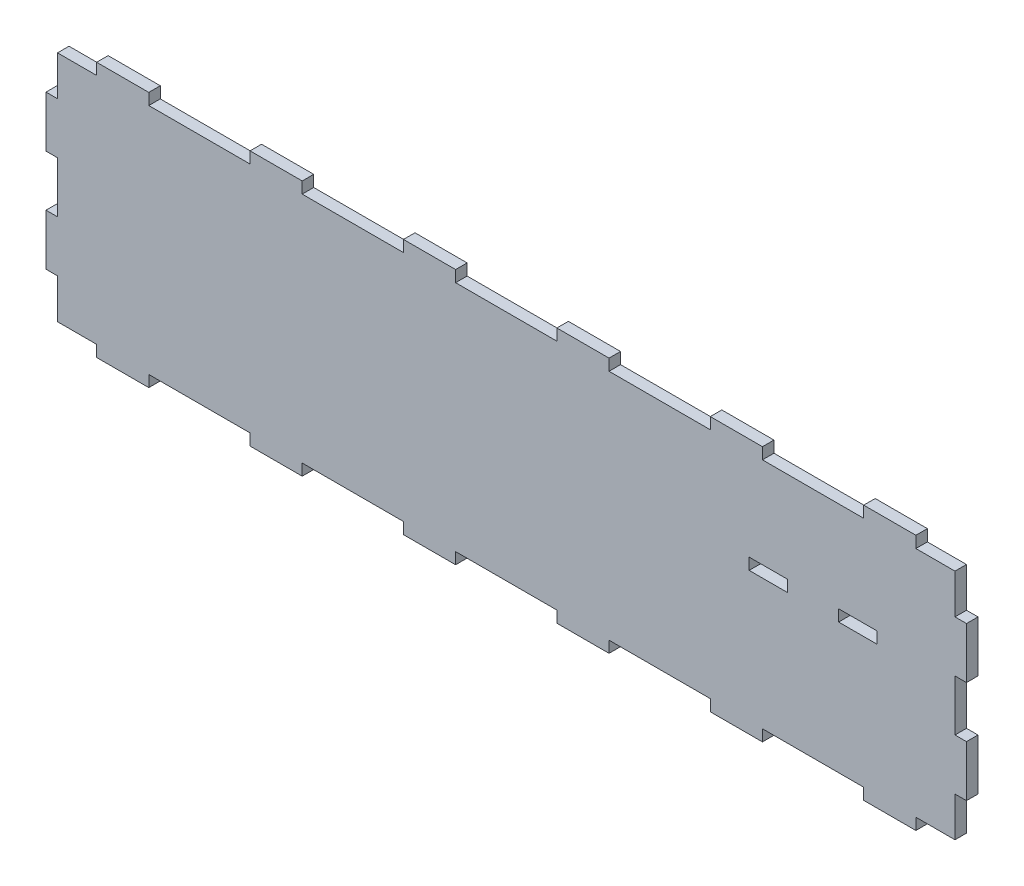
SolidWorks part; units mm, degrees
ref_plane "Front Plane" through (0, 0, 0) normal (0, 0, 1) x (1, 0, 0)
ref_plane "Top Plane" through (0, 0, 0) normal (0, 1, 0) x (1, 0, 0)
ref_plane "Right Plane" through (0, 0, 0) normal (1, 0, 0) x (0, 0, -1)
sketch "Sketch1" plane through (0, 0, 0) normal (0, 0, 1) x (1, 0, 0)
  line L1 (-228.6, -63.5) -> (228.6, -63.5)
  line L2 (-228.6, -63.5) -> (-228.6, 63.5)
  line L3 (-228.6, 63.5) -> (228.6, 63.5)
  line L4 (228.6, -63.5) -> (228.6, 63.5)
  line L5 (-228.6, -63.5) -> (228.6, 63.5) construction
  line L6 (-228.6, 63.5) -> (228.6, -63.5) construction
  point P0 (0, 0)
  dimension "D1" = 457.2
  dimension "D2" = 127
extrude "Boss-Extrude1" add sketch "Sketch1" along normal blind 5.715
sketch "Sketch2" plane through (0, 0, 5.715) normal (0, 0, 1) x (1, 0, 0)
  line L1 (165.1, 12.7) -> (184.15, 12.7)
  line L2 (165.1, 12.7) -> (165.1, 6.985)
  line L3 (165.1, 6.985) -> (184.15, 6.985)
  line L4 (184.15, 12.7) -> (184.15, 6.985)
  line L5 (120.65, 12.7) -> (139.7, 12.7)
  line L6 (120.65, 12.7) -> (120.65, 6.985)
  line L7 (120.65, 6.985) -> (139.7, 6.985)
  line L8 (139.7, 12.7) -> (139.7, 6.985)
  line L9 (139.7, 12.7) -> (165.1, 12.7) construction
  line L11 (152.4, 12.7) -> (152.4, 6.985) construction
  line L12 (139.7, 6.985) -> (165.1, 6.985) construction
  line L13 (228.6, -63.5) -> (228.6, 63.5) construction
  line L14 (139.7, 9.8425) -> (165.1, 9.8425) construction
  line L15 (228.6, 63.5) -> (-228.6, 63.5) construction
  point P9 (152.4, 12.7)
  dimension "D1" = 25.4
  dimension "D2" = 19.05
  dimension "D3" = 5.715
  dimension "D4" = 76.2
  dimension "D5" = 50.8
extrude "LED Mount Holes" cut sketch "Sketch2" against normal through all
sketch "Sketch4" plane through (0, 0, 0) normal (0, 0, -1) x (-1, 0, 0)
  line L0 (-222.885, 38.1) -> (-222.885, 12.7) construction
  line L1 (-228.6, 63.5) -> (-222.885, 63.5)
  line L2 (-228.6, 63.5) -> (-228.6, 38.1)
  line L3 (-228.6, 38.1) -> (-222.885, 38.1)
  line L4 (-222.885, 63.5) -> (-222.885, 38.1)
  line L5 (-228.6, 12.7) -> (-222.885, 12.7)
  line L6 (-228.6, 12.7) -> (-228.6, -12.7)
  line L7 (-228.6, -12.7) -> (-222.885, -12.7)
  line L8 (-222.885, 12.7) -> (-222.885, -12.7)
  line L9 (-222.885, -12.7) -> (-222.885, -38.1) construction
  line L10 (-228.6, -63.5) -> (-228.6, 63.5) construction
  line L11 (-228.6, -38.1) -> (-222.885, -38.1)
  line L12 (-228.6, -38.1) -> (-228.6, -63.5)
  line L13 (-228.6, -63.5) -> (-222.885, -63.5)
  line L14 (-222.885, -38.1) -> (-222.885, -63.5)
  dimension "D1" = 5.715
  dimension "D2" = 25.4
extrude "Cut-Extrude2" cut sketch "Sketch4" against normal through all
mirror "Mirror1" about plane through (0, 0, 0) normal (1, 0, 0) of "Cut-Extrude2"
sketch "Sketch5" plane through (0, 0, 0) normal (0, 0, -1) x (-1, 0, 0)
  line L0 (-222.885, 63.5) -> (222.885, 63.5) construction
  line L1 (-177.8, 63.5) -> (-127, 63.5)
  line L2 (-177.8, 63.5) -> (-177.8, 57.8358)
  line L3 (-177.8, 57.8358) -> (-127, 57.8358)
  line L4 (-127, 63.5) -> (-127, 57.8358)
  line L6 (-101.6, 57.8358) -> (-50.8, 57.8358)
  line L7 (-50.8, 63.5) -> (-50.8, 57.8358)
  line L8 (-101.6, 63.5) -> (-50.8, 63.5)
  line L9 (-101.6, 63.5) -> (-101.6, 57.8358)
  line L10 (-25.4, 57.8358) -> (25.4, 57.8358)
  line L11 (25.4, 63.5) -> (25.4, 57.8358)
  line L12 (-25.4, 63.5) -> (25.4, 63.5)
  line L13 (-25.4, 63.5) -> (-25.4, 57.8358)
  line L14 (50.8, 57.8358) -> (101.6, 57.8358)
  line L15 (101.6, 63.5) -> (101.6, 57.8358)
  line L16 (50.8, 63.5) -> (101.6, 63.5)
  line L17 (50.8, 63.5) -> (50.8, 57.8358)
  line L18 (127, 57.8358) -> (177.8, 57.8358)
  line L19 (177.8, 63.5) -> (177.8, 57.8358)
  line L20 (127, 63.5) -> (177.8, 63.5)
  line L21 (127, 63.5) -> (127, 57.8358)
  line L22 (203.2, 57.8358) -> (254, 57.8358)
  line L23 (254, 63.5) -> (254, 57.8358)
  line L24 (203.2, 63.5) -> (254, 63.5)
  line L25 (203.2, 63.5) -> (203.2, 57.8358)
  line L31 (-228.6, 12.7) -> (-228.6, 38.1) construction
  line L32 (-228.6, 57.785) -> (-203.2, 57.785)
  line L33 (-228.6, 57.785) -> (-228.6, 63.5)
  line L34 (-228.6, 63.5) -> (-203.2, 63.5)
  line L35 (-203.2, 57.785) -> (-203.2, 63.5)
  line L36 (279.4, 57.8358) -> (330.2, 57.8358) [skipped]
  line L37 (330.2, 63.5) -> (330.2, 57.8358) [skipped]
  line L38 (279.4, 63.5) -> (330.2, 63.5) [skipped]
  line L39 (279.4, 63.5) -> (279.4, 57.8358) [skipped]
  dimension "D1" = 25.4
  dimension "D2" = 5.6642
  dimension "D3" = 50.8
  dimension "D5" = 25.4
  dimension "D6" = 5.715
  dimension "D7" = 25.4
  dimension "D4" = 7
extrude "Cut-Extrude3" cut sketch "Sketch5" against normal through all
sketch "Sketch6" plane through (0, 0, 0) normal (0, 0, -1) x (-1, 0, 0)
  line L0 (-222.885, 57.785) -> (-203.2, 57.785) construction
  line L1 (-203.2, 63.5) -> (-203.454, 63.5)
  line L2 (-203.2, 63.5) -> (-203.2, 57.785)
  line L3 (-203.2, 57.785) -> (-203.454, 57.785)
  line L4 (-203.454, 63.5) -> (-203.454, 57.785)
  line L5 (-177.8, 57.8358) -> (-127, 57.8358) construction
  line L6 (-177.8, 63.5) -> (-177.546, 63.5)
  line L7 (-177.8, 63.5) -> (-177.8, 57.785)
  line L8 (-177.8, 57.785) -> (-177.546, 57.785)
  line L9 (-177.546, 63.5) -> (-177.546, 57.785)
  line L10 (-127, 63.5) -> (-127.254, 63.5)
  line L11 (-127, 63.5) -> (-127, 57.8358)
  line L12 (-127, 57.8358) -> (-127.254, 57.8358)
  line L13 (-127.254, 63.5) -> (-127.254, 57.8358)
  line L14 (-101.6, 57.8358) -> (-50.8, 57.8358) construction
  line L15 (-101.6, 63.5) -> (-101.346, 63.5)
  line L16 (-101.6, 63.5) -> (-101.6, 57.8358)
  line L17 (-101.6, 57.8358) -> (-101.346, 57.8358)
  line L18 (-101.346, 63.5) -> (-101.346, 57.8358)
  line L19 (-50.8, 63.5) -> (-51.054, 63.5)
  line L20 (-50.8, 63.5) -> (-50.8, 57.8358)
  line L21 (-50.8, 57.8358) -> (-51.054, 57.8358)
  line L22 (-51.054, 63.5) -> (-51.054, 57.8358)
  line L23 (-25.4, 57.8358) -> (25.4, 57.8358) construction
  line L24 (-25.4, 63.5) -> (-25.146, 63.5)
  line L25 (-25.4, 63.5) -> (-25.4, 57.8358)
  line L26 (-25.4, 57.8358) -> (-25.146, 57.8358)
  line L27 (-25.146, 63.5) -> (-25.146, 57.8358)
  line L28 (50.8, 57.8358) -> (101.6, 57.8358) construction
  line L29 (25.4, 63.5) -> (25.146, 63.5)
  line L30 (25.4, 63.5) -> (25.4, 57.8358)
  line L31 (25.4, 57.8358) -> (25.146, 57.8358)
  line L32 (25.146, 63.5) -> (25.146, 57.8358)
  line L33 (50.8, 63.5) -> (51.054, 63.5)
  line L34 (50.8, 63.5) -> (50.8, 57.8358)
  line L35 (50.8, 57.8358) -> (51.054, 57.8358)
  line L36 (51.054, 63.5) -> (51.054, 57.8358)
  line L37 (127, 57.8358) -> (177.8, 57.8358) construction
  line L38 (101.6, 63.5) -> (101.346, 63.5)
  line L39 (101.6, 63.5) -> (101.6, 57.8358)
  line L40 (101.6, 57.8358) -> (101.346, 57.8358)
  line L41 (101.346, 63.5) -> (101.346, 57.8358)
  line L42 (127, 63.5) -> (127.254, 63.5)
  line L43 (127, 63.5) -> (127, 57.8358)
  line L44 (127, 57.8358) -> (127.254, 57.8358)
  line L45 (127.254, 63.5) -> (127.254, 57.8358)
  line L46 (203.2, 57.8358) -> (222.885, 57.8358) construction
  line L47 (177.8, 63.5) -> (177.546, 63.5)
  line L48 (177.8, 63.5) -> (177.8, 57.8358)
  line L49 (177.8, 57.8358) -> (177.546, 57.8358)
  line L50 (177.546, 63.5) -> (177.546, 57.8358)
  line L51 (203.2, 63.5) -> (203.454, 63.5)
  line L52 (203.2, 63.5) -> (203.2, 57.8358)
  line L53 (203.2, 57.8358) -> (203.454, 57.8358)
  line L54 (203.454, 63.5) -> (203.454, 57.8358)
  dimension "D1" = 0.254
extrude "Boss-Extrude2" add sketch "Sketch6" against normal up to surface (5.715 mm away) up to face at (0, 32.8318, 5.715)
mirror "Mirror2" about plane through (0, 0, 0) normal (0, 1, 0) of "Cut-Extrude3", "Boss-Extrude2"
sketch "Sketch7" [suppressed] plane through (0, 0, 0) normal (0, 0, -1) x (-1, 0, 0)
  line L1 (-139.065, -25.9715) -> (-116.84, -25.9715)
  line L2 (-139.065, -25.9715) -> (-139.065, -48.1965)
  line L3 (-139.065, -48.1965) -> (-116.84, -48.1965)
  line L4 (-116.84, -25.9715) -> (-116.84, -48.1965)
  line L5 (-120.65, 12.7) -> (-120.65, 6.985) construction
  line L6 (-127.9525, -25.9715) -> (-127.9525, -37.084) construction
  line L7 (-127.9525, -37.084) -> (-116.84, -37.084) construction
  line L8 (-101.346, -63.5) -> (-127.254, -63.5) construction
  circle A0 centre (-127.9525, -37.084) radius 25.4 construction
  circle A1 centre (-127.9525, -37.084) radius 19.05 construction
  circle A2 centre (-127.9525, -18.034) radius 1.905
  dimension "D4" = 50.8
  dimension "D5" = 6.35
  dimension "D6" = 3.81
  dimension "D1" = 22.225
  dimension "D2" = 1.016
  dimension "D3" = 3.81
extrude "Cut-Extrude4" [suppressed] cut sketch "Sketch7" against normal through all
